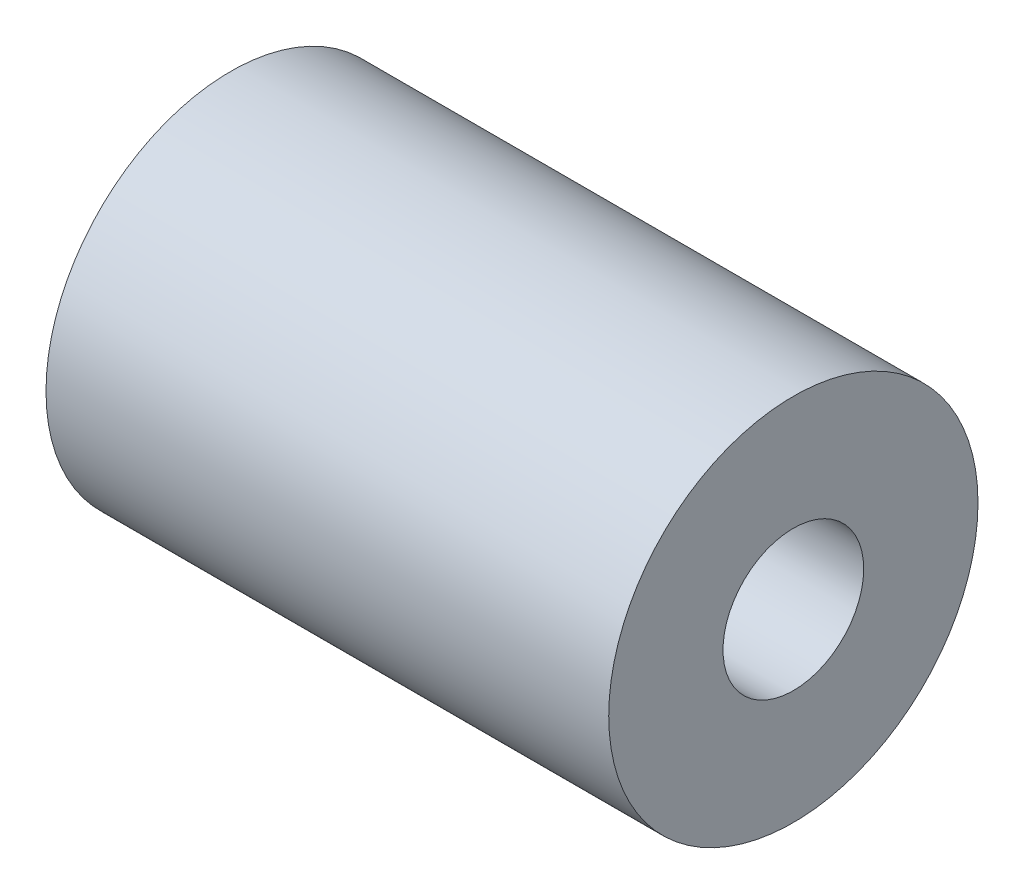
SolidWorks part; units mm, degrees
material "AISI 1020"
ref_plane "Front Plane" through (0, 0, 0) normal (0, 0, 1) x (1, 0, 0)
ref_plane "Top Plane" through (0, 0, 0) normal (0, 1, 0) x (1, 0, 0)
ref_plane "Right Plane" through (0, 0, 0) normal (1, 0, 0) x (0, 0, -1)
sketch "Sketch1" plane through (0, 0, 0) normal (1, 0, 0) x (0, 0, -1)
  circle A0 centre (0, 0) radius 16.6687
  dimension "D1" = 33.3375
extrude "Extrude1" add sketch "Sketch1" along normal blind 50.8
sketch "Sketch2" plane through (50.8, 0, 0) normal (1, 0, 0) x (0, 0, -1)
  circle A0 centre (0, 0) radius 6.35
  dimension "D1" = 12.7
extrude "Cut-Extrude1" cut sketch "Sketch2" against normal blind 25.4
sketch "Sketch3" plane through (0, 0, 0) normal (-1, 0, 0) x (0, 0, 1)
  circle A0 centre (0, 0) radius 7.9375
  dimension "D1" = 15.875
extrude "Cut-Extrude2" cut sketch "Sketch3" against normal blind 25.4
